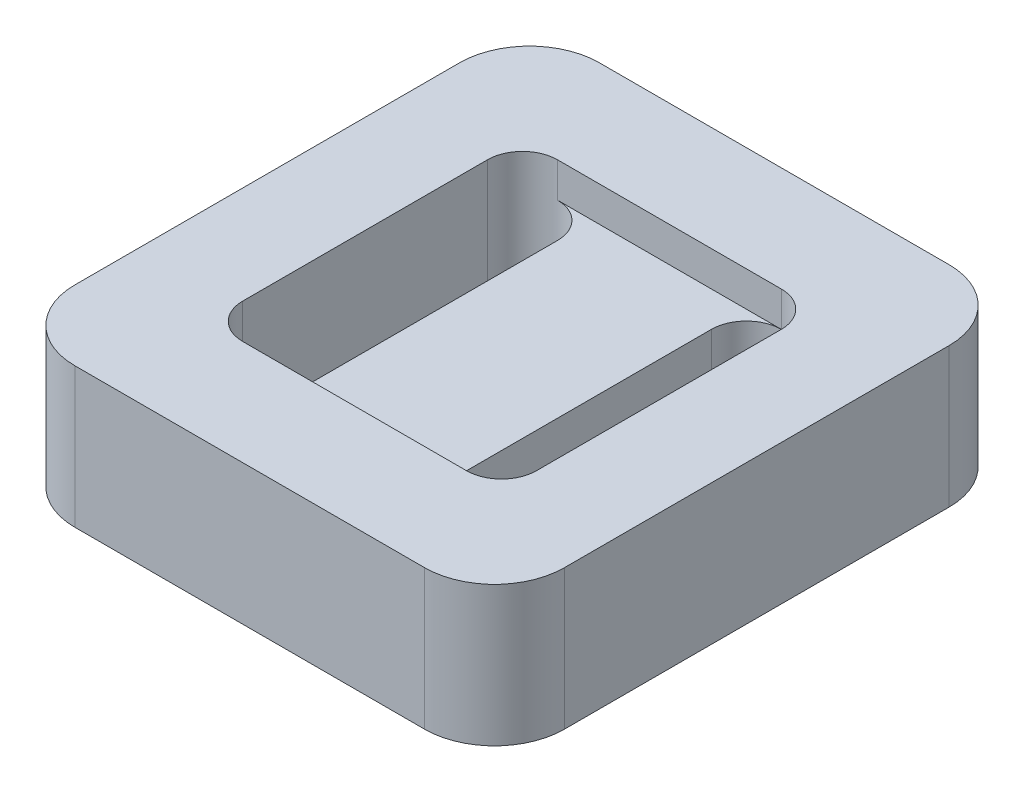
SolidWorks part; units mm, degrees
material "Pure Lead"
ref_plane "Front Plane" through (0, 0, 0) normal (0, 0, 1) x (1, 0, 0)
ref_plane "Top Plane" through (0, 0, 0) normal (0, 1, 0) x (1, 0, 0)
ref_plane "Right Plane" through (0, 0, 0) normal (1, 0, 0) x (0, 0, -1)
sketch "Sketch1" plane through (0, 0, 0) normal (0, 1, 0) x (1, 0, 0)
  line L0 (-16, -17.5) -> (-16, 17.5) construction
  line L1 (-25, -37.5) -> (25, -37.5)
  line L2 (-35, -27.5) -> (-35, 27.5)
  line L3 (-25, 37.5) -> (25, 37.5)
  line L4 (35, -27.5) -> (35, 27.5)
  line L5 (-35, -37.5) -> (35, 37.5) construction
  line L6 (-35, 37.5) -> (35, -37.5) construction
  line L7 (-21, -17.5) -> (-21, 17.5)
  line L8 (-11, -17.5) -> (-11, 17.5)
  line L9 (0, -22.5647) -> (0, 22.5647) construction
  line L10 (16, -17.5) -> (16, 17.5) construction
  line L11 (21, -17.5) -> (21, 17.5)
  line L12 (11, -17.5) -> (11, 17.5)
  arc A0 (-21, -17.5) -> (-11, -17.5) centre (-16, -17.5) ccw
  arc A1 (-11, 17.5) -> (-21, 17.5) centre (-16, 17.5) ccw
  arc A2 (21, -17.5) -> (11, -17.5) centre (16, -17.5) cw
  arc A3 (11, 17.5) -> (21, 17.5) centre (16, 17.5) cw
  arc A4 (-25, -37.5) -> (-35, -27.5) centre (-25, -27.5) cw
  arc A5 (25, -37.5) -> (35, -27.5) centre (25, -27.5) ccw
  arc A6 (35, 27.5) -> (25, 37.5) centre (25, 27.5) ccw
  arc A7 (-35, 27.5) -> (-25, 37.5) centre (-25, 27.5) cw
  point P0 (0, 0)
  point P8 (-16, 0)
  point P15 (16, 0)
  point P18 (0, 0)
  dimension "D6" = 10
  dimension "D1" = 70
  dimension "D2" = 75
  dimension "D3" = 35
  dimension "D4" = 14
  dimension "D5" = 10
extrude "Boss-Extrude1" add sketch "Sketch1" along normal blind 20
sketch "Sketch2" plane through (0, 20, 0) normal (0, 1, 0) x (1, 0, 0)
  line L0 (-21, 17.5) -> (-21, -17.5) construction
  line L1 (-11, -17.5) -> (-11, 17.5) construction
  line L2 (11, 17.5) -> (11, -17.5) construction
  line L3 (21, -17.5) -> (21, 17.5) construction
  line L4 (-25, -37.5) -> (25, -37.5)
  line L5 (35, -27.5) -> (35, 27.5)
  line L6 (25, 37.5) -> (-25, 37.5)
  line L7 (-35, 27.5) -> (-35, -27.5)
  line L8 (-25, -37.5) -> (25, -37.5)
  line L9 (35, -27.5) -> (35, 27.5)
  line L10 (25, 37.5) -> (-25, 37.5)
  line L11 (-35, 27.5) -> (-35, -27.5)
  line L12 (21, -17.5) -> (21, 17.5)
  line L13 (11, 17.5) -> (11, -17.5)
  line L14 (-11, -17.5) -> (-11, 17.5)
  line L15 (-21, 17.5) -> (-21, -17.5)
  line L16 (-16, 22.5) -> (16, 22.5)
  line L17 (-16, -22.5) -> (16, -22.5)
  arc A0 (-11, 17.5) -> (-21, 17.5) centre (-16, 17.5) ccw construction
  arc A1 (-21, -17.5) -> (-11, -17.5) centre (-16, -17.5) ccw construction
  arc A2 (11, -17.5) -> (21, -17.5) centre (16, -17.5) ccw construction
  arc A3 (21, 17.5) -> (11, 17.5) centre (16, 17.5) ccw construction
  arc A4 (-35, -27.5) -> (-25, -37.5) centre (-25, -27.5) ccw
  arc A5 (25, -37.5) -> (35, -27.5) centre (25, -27.5) ccw
  arc A6 (35, 27.5) -> (25, 37.5) centre (25, 27.5) ccw
  arc A7 (-25, 37.5) -> (-35, 27.5) centre (-25, 27.5) ccw
  arc A8 (-35, -27.5) -> (-25, -37.5) centre (-25, -27.5) ccw
  arc A9 (25, -37.5) -> (35, -27.5) centre (25, -27.5) ccw
  arc A10 (35, 27.5) -> (25, 37.5) centre (25, 27.5) ccw
  arc A11 (-25, 37.5) -> (-35, 27.5) centre (-25, 27.5) ccw
  arc A12 (21, 17.5) -> (11, 17.5) centre (16, 17.5) ccw
  arc A13 (11, -17.5) -> (21, -17.5) centre (16, -17.5) ccw
  arc A14 (-21, -17.5) -> (-11, -17.5) centre (-16, -17.5) ccw
  arc A15 (-11, 17.5) -> (-21, 17.5) centre (-16, 17.5) ccw
  arc M17 (-11, -17.5) -> (-21, -17.5) centre (-16, -17.5) cw
  arc M19 (-21, 17.5) -> (-11, 17.5) centre (-16, 17.5) cw
  line M20 (-11, 17.5) -> (-11, -17.5)
  arc M29 (21, -17.5) -> (11, -17.5) centre (16, -17.5) cw
  line M30 (11, -17.5) -> (11, 17.5)
  arc M31 (11, 17.5) -> (21, 17.5) centre (16, 17.5) cw
  dimension "D1" = 0
extrude "Cut-Extrude1" cut sketch "Sketch2" against normal blind 5 contours L17 L16 M17 M29 M30 M31 M19 M20
